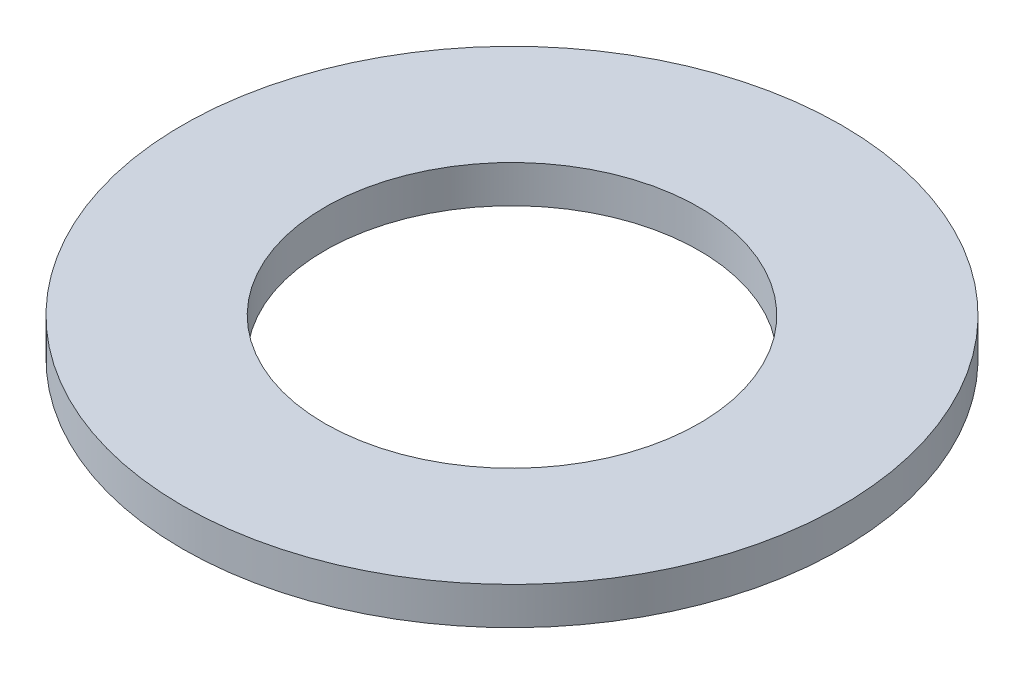
SolidWorks part; units mm, degrees
ref_plane "Front Plane" through (0, 0, 0) normal (0, 0, 1) x (1, 0, 0)
ref_plane "Top Plane" through (0, 0, 0) normal (0, 1, 0) x (1, 0, 0)
ref_plane "Right Plane" through (0, 0, 0) normal (1, 0, 0) x (0, 0, -1)
sketch "Sketch1" plane through (0, 0, 0) normal (0, 1, 0) x (1, 0, 0)
  circle A0 centre (0, 0) radius 12.5
  circle A1 centre (0, 0) radius 22
  dimension "D1" = 44
  dimension "D2" = 25
extrude "Boss-Extrude1" add sketch "Sketch1" along normal blind 2.5 contours A0 | A1
